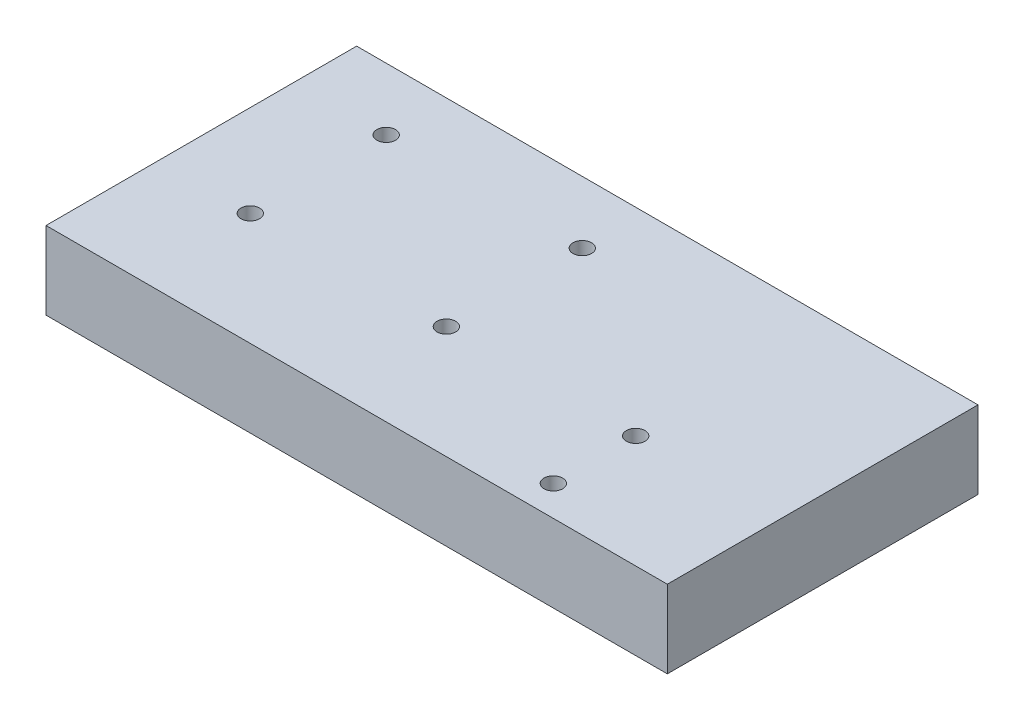
SolidWorks part; units mm, degrees
ref_plane "Front Plane" through (0, 0, 0) normal (0, 0, 1) x (1, 0, 0)
ref_plane "Top Plane" through (0, 0, 0) normal (0, 1, 0) x (1, 0, 0)
ref_plane "Right Plane" through (0, 0, 0) normal (1, 0, 0) x (0, 0, -1)
sketch "Sketch1" plane through (0, 0, 0) normal (0, 1, 0) x (1, 0, 0)
  line L1 (0, 0) -> (80, 0)
  line L2 (0, 0) -> (0, 40)
  line L3 (0, 40) -> (80, 40)
  line L4 (80, 0) -> (80, 40)
  line L5 (11.8, 32) -> (37.05, 32) construction
  line L6 (11.8, 32) -> (11.8, 14.5) construction
  line L7 (11.8, 14.5) -> (37.05, 14.5) construction
  line L8 (37.05, 32) -> (37.05, 14.5) construction
  point P9 (61.425, 14.5)
  point P10 (24.425, 14.5)
  dimension "D1" = 40
  dimension "D2" = 80
  dimension "D3" = 8
  dimension "D4" = 11.8
  dimension "D5" = 17.5
  dimension "D6" = 25.25
  dimension "D7" = 37
extrude "Boss-Extrude1" add sketch "Sketch1" against normal blind 10
sketch "Sketch4" plane through (0, 0, 0) normal (0, 1, 0) x (1, 0, 0)
  line L1 (0, 0) -> (80, 0) construction
  point P0 (11.8, 32)
  point P3 (37.05, 32)
  point P6 (37.05, 14.5)
  point P9 (11.8, 14.5)
  point P12 (61.425, 14.5)
  point P17 (61.425, 3.9)
  point P22 (0, 0)
  dimension "D1" = 3.9
hole_wizard "M2 Clearance Hole1" positions "Sketch4" profile "Sketch3" hole size "M2" standard "ISO"
sketch "Sketch3" plane through (11.8, 0, -32) normal (1, 0, 0) x (0, 0, 1)
  line L0 (0, 0) -> (0, 6.721)
  line L1 (0, 6.721) -> (1.2, 6)
  line L2 (1.2, 6) -> (1.2, 0)
  line L5 (1.2, 0) -> (0, 0)
  line L10 (0, 6.721) -> (-1.2, 6) construction
  line L11 (0, -6.35) -> (0, 107.95) construction
  dimension "Hole Dia." = 2.4
  dimension "Hole Depth" = 6
  dimension "Drill Angle" = 118
